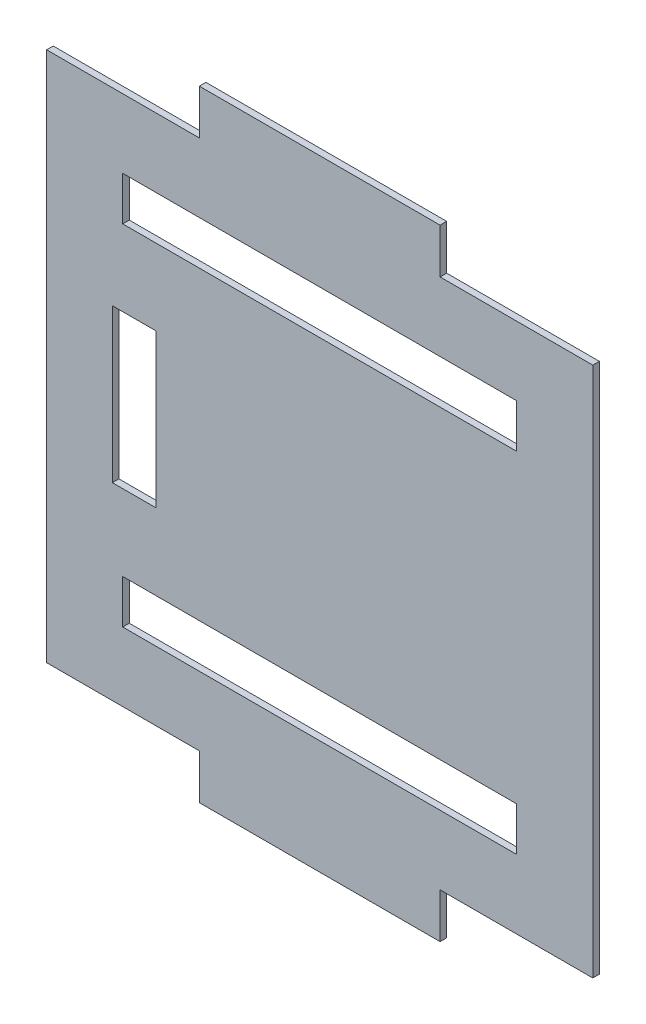
SolidWorks part; units mm, degrees
ref_plane "Plan de face" through (0, 0, 0) normal (0, 0, 1) x (1, 0, 0)
ref_plane "Plan de dessus" through (0, 0, 0) normal (0, 1, 0) x (1, 0, 0)
ref_plane "Plan de droite" through (0, 0, 0) normal (1, 0, 0) x (0, 0, -1)
sketch "Esquisse1" plane through (0, 0, 0) normal (0, 0, 1) x (1, 0, 0)
  line L0 (0, 0) -> (-200, 0)
  line L5 (-200, 0) -> (-224.7487, 24.7487)
  line L6 (-224.7487, 24.7487) -> (-224.7487, 284.7487)
  line L7 (-224.7487, 284.7487) -> (-200, 309.4975)
  line L8 (-200, 309.4975) -> (0, 309.4975)
  line L9 (0, 309.4975) -> (24.7487, 284.7487)
  line L10 (24.7487, 284.7487) -> (24.7487, 24.7487)
  line L11 (24.7487, 24.7487) -> (0, 0)
  dimension "D1" = 260
  dimension "D2" = 35
  dimension "D3" = 135
  dimension "D4" = 200
extrude "Base" add sketch "Esquisse1" along normal blind 3
sketch "Esquisse2" plane through (0, 0, 3) normal (0, 0, 1) x (1, 0, 0)
  line L0 (-100, 309.4975) -> (-100, 0) construction
  line L1 (0, 309.4975) -> (-200, 309.4975) construction
  line L2 (-200, 0) -> (0, 0) construction
  line L9 (-224.7487, 154.7487) -> (24.7487, 154.7487) construction
  line L10 (-224.7487, 284.7487) -> (-224.7487, 24.7487) construction
  line L11 (24.7487, 24.7487) -> (24.7487, 284.7487) construction
  line L18 (-45, 33.5) -> (-45, 13) construction
  line L21 (-155, 33.5) -> (-155, 13) construction
  line L25 (-45, 13) -> (-155, 13)
  line L28 (-224.7487, 33.5) -> (-155, 33.5)
  line L29 (-155, 33.5) -> (-155, 13)
  line L30 (-45, 13) -> (-45, 33.5)
  line L31 (-45, 33.5) -> (24.7487, 33.5)
  line L32 (-224.7487, 33.5) -> (-224.7487, 0)
  line L33 (-224.7487, 0) -> (24.7487, 0)
  line L34 (24.7487, 0) -> (24.7487, 33.5)
  line L41 (-155, 275.9975) -> (-155, 296.4975) construction
  line L42 (-45, 275.9975) -> (-45, 296.4975) construction
  line L43 (24.7487, 309.4975) -> (24.7487, 275.9975)
  line L44 (-224.7487, 309.4975) -> (24.7487, 309.4975)
  line L45 (-224.7487, 275.9975) -> (-224.7487, 309.4975)
  line L46 (-45, 275.9975) -> (24.7487, 275.9975)
  line L47 (-45, 296.4975) -> (-45, 275.9975)
  line L48 (-155, 275.9975) -> (-155, 296.4975)
  line L49 (-224.7487, 275.9975) -> (-155, 275.9975)
  line L50 (-45, 296.4975) -> (-155, 296.4975)
  dimension "D1" = 110
  dimension "D2" = 13
  dimension "D3" = 33.5
  dimension "D4" = 33.5
  dimension "D5" = 55
extrude "profilés" cut sketch "Esquisse2" against normal blind 3
sketch "Esquisse3" plane through (0, 0, 3) normal (0, 0, 1) x (1, 0, 0)
  line L0 (-100, 13) -> (-100, 296.4975) construction
  line L1 (-190, 244.4975) -> (-10, 244.4975)
  line L2 (-190, 244.4975) -> (-190, 224.4975)
  line L3 (-190, 224.4975) -> (-10, 224.4975)
  line L4 (-10, 244.4975) -> (-10, 224.4975)
  line L7 (-224.7487, 154.7487) -> (24.7487, 154.7487) construction
  line L8 (-45, 13) -> (-155, 13) construction
  line L9 (-155, 296.4975) -> (-45, 296.4975) construction
  line L10 (-224.7487, 275.9975) -> (-224.7487, 33.5) construction
  line L11 (24.7487, 33.5) -> (24.7487, 275.9975) construction
  line L12 (-100, 244.4975) -> (-100, 224.4975) construction
  line L14 (-10, 65) -> (-10, 85)
  line L15 (-190, 85) -> (-10, 85)
  line L16 (-190, 65) -> (-190, 85)
  line L17 (-190, 65) -> (-10, 65)
  line L18 (-194.7487, 154.7487) -> (-174.7487, 154.7487) construction
  line L19 (-194.7487, 189.7487) -> (-174.7487, 189.7487)
  line L20 (-194.7487, 189.7487) -> (-194.7487, 119.7487)
  line L21 (-194.7487, 119.7487) -> (-174.7487, 119.7487)
  line L22 (-174.7487, 189.7487) -> (-174.7487, 119.7487)
  dimension "D1" = 180
  dimension "D2" = 20
  dimension "D3" = 52
  dimension "D4" = 20
  dimension "D5" = 70
  dimension "D6" = 30
  dimension "D7" = 90
extrude "Enlèv. mat.-Extru.1" cut sketch "Esquisse3" against normal blind 3
